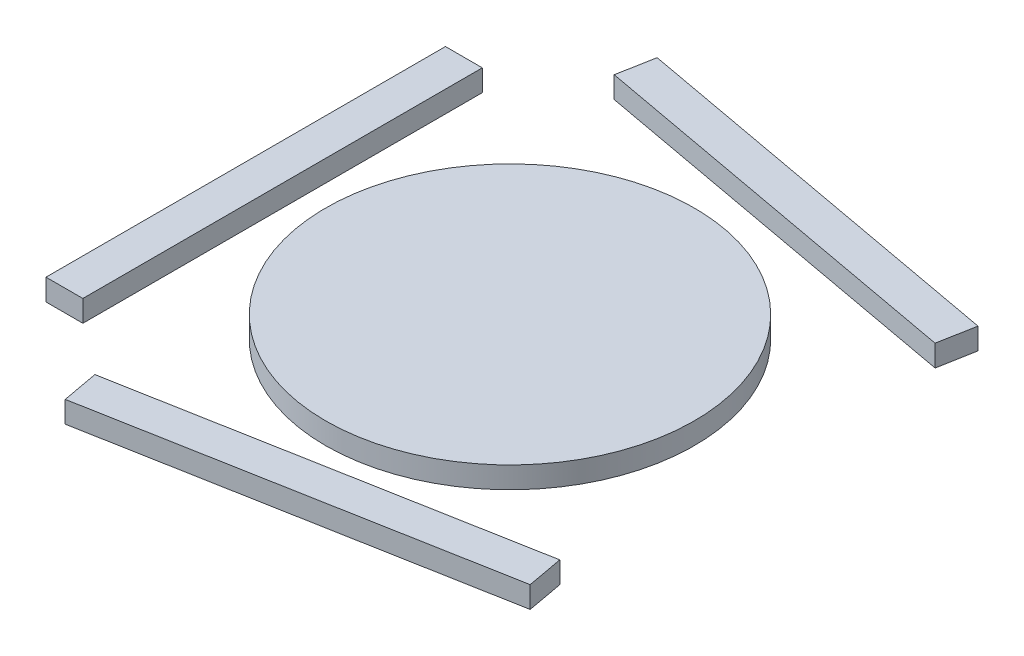
SolidWorks part; units mm, degrees
ref_plane "Front Plane" through (0, 0, 0) normal (0, 0, 1) x (1, 0, 0)
ref_plane "Top Plane" through (0, 0, 0) normal (0, 1, 0) x (1, 0, 0)
ref_plane "Right Plane" through (0, 0, 0) normal (1, 0, 0) x (0, 0, -1)
sketch "Sketch1" plane through (0, 0, 0) normal (0, 1, 0) x (1, 0, 0)
  line L0 (386.3934, 305.3279) -> (-252.9508, 422.541) construction
  line L1 (-242.1311, 481.5574) -> (-252.9508, 422.541) construction
  line L2 (397.2131, 364.3443) -> (-242.1311, 481.5574) construction
  line L3 (397.2131, 364.3443) -> (386.3934, 305.3279) construction
  line L4 (-430, 325) -> (-370, 325) construction
  line L5 (-370, -325) -> (-370, 325) construction
  line L6 (-430, -325) -> (-430, 325) construction
  line L7 (-430, -325) -> (-370, -325) construction
  line L8 (-242.1311, -481.5574) -> (-252.9508, -422.541) construction
  line L9 (-252.9508, -422.541) -> (386.3934, -305.3279) construction
  line L10 (-242.1311, -481.5574) -> (397.2131, -364.3443) construction
  line L11 (397.2131, -364.3443) -> (386.3934, -305.3279) construction
  line L12 (286.7428, 456.4028) -> (517.326, -151.3236) construction
  line L13 (286.7428, 456.4028) -> (230.645, 435.1182) construction
  line L14 (230.645, 435.1182) -> (461.2282, -172.6082) construction
  line L15 (517.326, -151.3236) -> (461.2282, -172.6082) construction
  line L16 (386.3934, 305.3279) -> (-252.9508, 422.541)
  line L17 (-242.1311, 481.5574) -> (-252.9508, 422.541)
  line L18 (397.2131, 364.3443) -> (-242.1311, 481.5574)
  line L19 (397.2131, 364.3443) -> (386.3934, 305.3279)
  line L20 (-430, 325) -> (-370, 325)
  line L21 (-370, -325) -> (-370, 325)
  line L22 (-430, -325) -> (-430, 325)
  line L23 (-430, -325) -> (-370, -325)
  line L24 (-242.1311, -481.5574) -> (-252.9508, -422.541)
  line L25 (-252.9508, -422.541) -> (386.3934, -305.3279)
  line L26 (-242.1311, -481.5574) -> (397.2131, -364.3443)
  line L27 (397.2131, -364.3443) -> (386.3934, -305.3279)
  line L28 (286.7428, 456.4028) -> (517.326, -151.3236) construction
  line L29 (286.7428, 456.4028) -> (230.645, 435.1182) construction
  line L30 (230.645, 435.1182) -> (461.2282, -172.6082) construction
  line L31 (517.326, -151.3236) -> (461.2282, -172.6082) construction
  circle A0 centre (0, 0) radius 300
  dimension "D1" = 600
extrude "Boss-Extrude1" add sketch "Sketch1" along normal blind 35
sketch "Sketch2" [suppressed] plane through (0, 0, 0) normal (0, 1, 0) x (1, 0, 0)
  line L0 (1150, 575) -> (-1150, 575) construction
  line L1 (-1150, 575) -> (-1150, -575) construction
  line L2 (1150, -575) -> (1150, 575) construction
  line L3 (-1150, -575) -> (1150, -575) construction
  line L4 (1150, 575) -> (-1150, 575)
  line L5 (-1150, 575) -> (-1150, -575)
  line L6 (1150, -575) -> (1150, 575)
  line L7 (-1150, -575) -> (1150, -575)
extrude "Boss-Extrude2" [suppressed] add sketch "Sketch2" along normal blind 30
